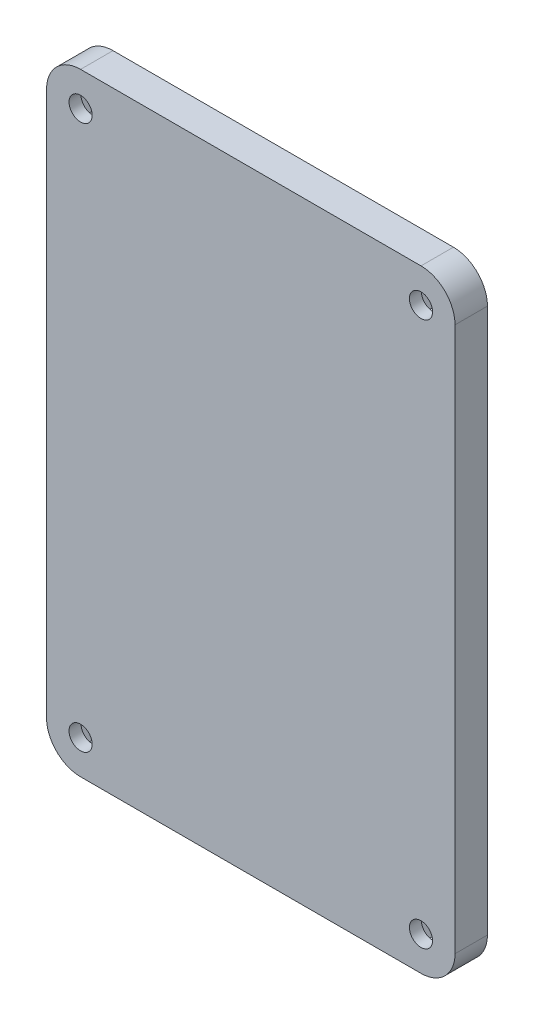
SolidWorks part; units mm, degrees
ref_plane "Front Plane" through (0, 0, 0) normal (0, 0, 1) x (1, 0, 0)
ref_plane "Top Plane" through (0, 0, 0) normal (0, 1, 0) x (1, 0, 0)
ref_plane "Right Plane" through (0, 0, 0) normal (1, 0, 0) x (0, 0, -1)
sketch "Sketch1" plane through (0, 0, 0) normal (0, 0, 1) x (1, 0, 0)
  line L1 (30, -45) -> (-30, -45)
  line L2 (30, -45) -> (30, 45)
  line L3 (30, 45) -> (-30, 45)
  line L4 (-30, -45) -> (-30, 45)
  line L5 (30, -45) -> (-30, 45) construction
  line L6 (30, 45) -> (-30, -45) construction
  point P0 (0, 0)
  dimension "D1" = 60
  dimension "D2" = 90
extrude "Boss-Extrude1" add sketch "Sketch1" along normal blind 4.7625
fillet "Fillet1" radius 5 4 edges at (-30, -45, 2.3813) (30, -45, 2.3813) (30, 45, 2.3813) (-30, 45, 2.3813)
sketch "Sketch2" plane through (0, 0, 0) normal (0, 0, 1) x (1, 0, 0)
  circle A0 centre (-25, 40) radius 1.7
  circle A1 centre (25, 40) radius 1.7
  circle A2 centre (25, -40) radius 1.7
  circle A3 centre (-25, -40) radius 1.7
  dimension "D1" = 3.4
extrude "Cut-Extrude1" cut sketch "Sketch2" along normal blind 5
sketch "Sketch3" plane through (0, 0, 0) normal (0, 0, 1) x (1, 0, 0)
  line L1 (-23.3834, 37.2) -> (-21.7668, 40)
  line L2 (-21.7668, 40) -> (-23.3834, 42.8)
  line L3 (-23.3834, 42.8) -> (-26.6166, 42.8)
  line L4 (-26.6166, 42.8) -> (-28.2332, 40)
  line L5 (-28.2332, 40) -> (-26.6166, 37.2)
  line L6 (-26.6166, 37.2) -> (-23.3834, 37.2)
  line L7 (26.6166, 37.2) -> (28.2332, 40)
  line L8 (28.2332, 40) -> (26.6166, 42.8)
  line L9 (26.6166, 42.8) -> (23.3834, 42.8)
  line L10 (23.3834, 42.8) -> (21.7668, 40)
  line L11 (21.7668, 40) -> (23.3834, 37.2)
  line L12 (23.3834, 37.2) -> (26.6166, 37.2)
  line L13 (26.6166, -42.8) -> (28.2332, -40)
  line L14 (28.2332, -40) -> (26.6166, -37.2)
  line L15 (26.6166, -37.2) -> (23.3834, -37.2)
  line L16 (23.3834, -37.2) -> (21.7668, -40)
  line L17 (21.7668, -40) -> (23.3834, -42.8)
  line L18 (23.3834, -42.8) -> (26.6166, -42.8)
  line L19 (-23.3834, -42.8) -> (-21.7668, -40)
  line L20 (-21.7668, -40) -> (-23.3834, -37.2)
  line L21 (-23.3834, -37.2) -> (-26.6166, -37.2)
  line L22 (-26.6166, -37.2) -> (-28.2332, -40)
  line L23 (-28.2332, -40) -> (-26.6166, -42.8)
  line L24 (-26.6166, -42.8) -> (-23.3834, -42.8)
  circle A0 centre (-25, 40) radius 2.8 construction
  circle A1 centre (25, 40) radius 2.8 construction
  circle A2 centre (25, -40) radius 2.8 construction
  circle A3 centre (-25, -40) radius 2.8 construction
  point P1 (-25, 42.8)
  dimension "D1" = 5.6
  dimension "D2" = 5.6
  dimension "D3" = 5.6
  dimension "D4" = 5.6
extrude "Cut-Extrude2" cut sketch "Sketch3" along normal blind 3
